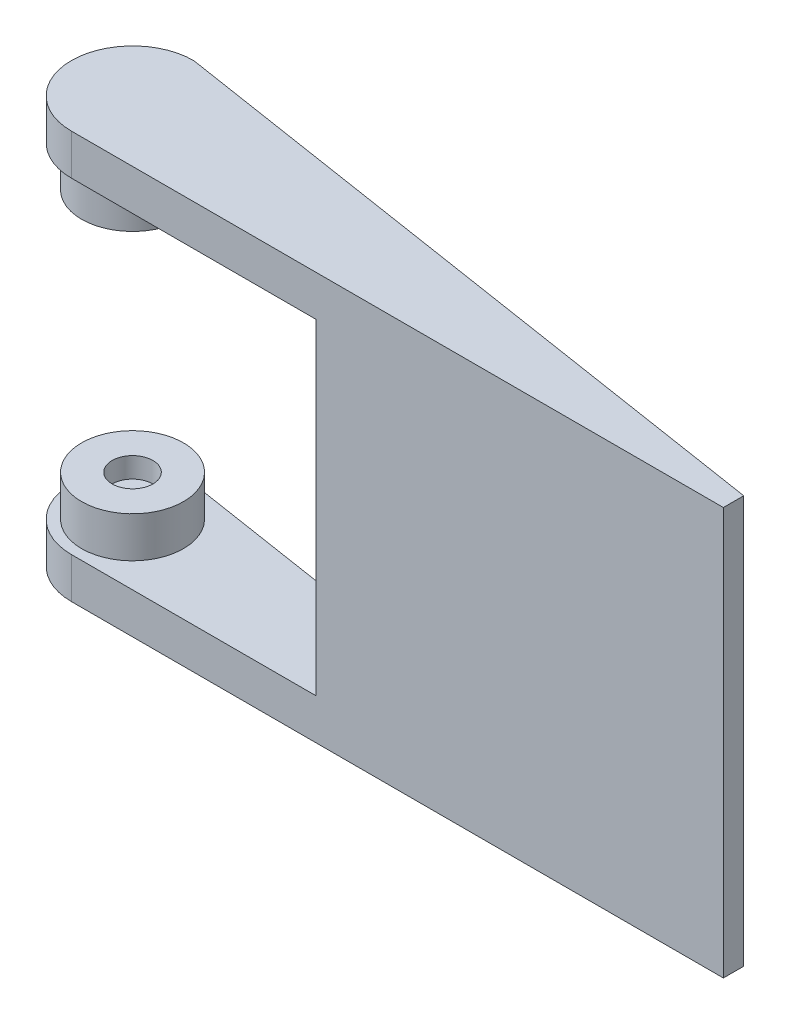
SolidWorks part; units mm, degrees
ref_plane "Front Plane" through (0, 0, 0) normal (0, 0, 1) x (1, 0, 0)
ref_plane "Top Plane" through (0, 0, 0) normal (0, 1, 0) x (1, 0, 0)
ref_plane "Right Plane" through (0, 0, 0) normal (1, 0, 0) x (0, 0, -1)
sketch "Sketch1" plane through (0, 0, 0) normal (0, 1, 0) x (1, 0, 0)
  line L0 (0, 15) -> (160, -10)
  line L1 (0, 15) -> (160, 15)
  line L2 (0, 15) -> (0, -15)
  line L3 (0, -15) -> (160, -15)
  line L4 (160, 15) -> (160, -15)
  circle A0 centre (0, 0) radius 15
  dimension "D1" = 30
  dimension "D2" = 160
  dimension "D3" = 30
  dimension "D4" = 5
extrude "Boss-Extrude1" add sketch "Sketch1" along normal blind 50 contours L2 A0 | L2 A0 L0 | A0 L3 L4 L0
sketch "Sketch2" plane through (0, 50, 0) normal (0, 1, 0) x (1, 0, 0)
  line L0 (0, -15) -> (160, -15)
  line L1 (160, -15) -> (160, -10)
  line L2 (160, -10) -> (0, 15)
  line L3 (60, -15) -> (60, 5.625)
  circle A0 centre (0, 0) radius 15
  circle A1 centre (0, 0) radius 12.5
  arc M4 (0, 15) -> (0, -15) centre (0, 0) ccw
  line M5 (0, -15) -> (160, -15)
  line M7 (160, -10) -> (0, 15)
  dimension "D1" = 30
  dimension "D4" = 25
  dimension "D2" = 15
  dimension "D3" = 100
extrude "Cut-Extrude1" cut sketch "Sketch2" against normal blind 40 contours A0 L3 L2 M5 | A0 A1 M4 M7
ref_plane "Plane1" through (0, 50, 0) normal (0, 1, 0) x (1, 0, 0)
sketch "Sketch3" plane through (0, 50, 0) normal (0, 1, 0) x (1, 0, 0)
  circle A0 centre (0, 0) radius 12.5
  dimension "D1" = 25
extrude "Cut-Extrude2" cut sketch "Sketch3" against normal blind 30
sketch "Sketch4" plane through (0, 20, 0) normal (0, 1, 0) x (1, 0, 0)
  circle A0 centre (0, 0) radius 5
  dimension "D1" = 10
extrude "Cut-Extrude3" cut sketch "Sketch4" against normal blind 5
mirror "Mirror1" about plane through (0, 50, 0) normal (0, 1, 0) of "Cut-Extrude3", "Cut-Extrude2", "Boss-Extrude1", "Cut-Extrude1"
